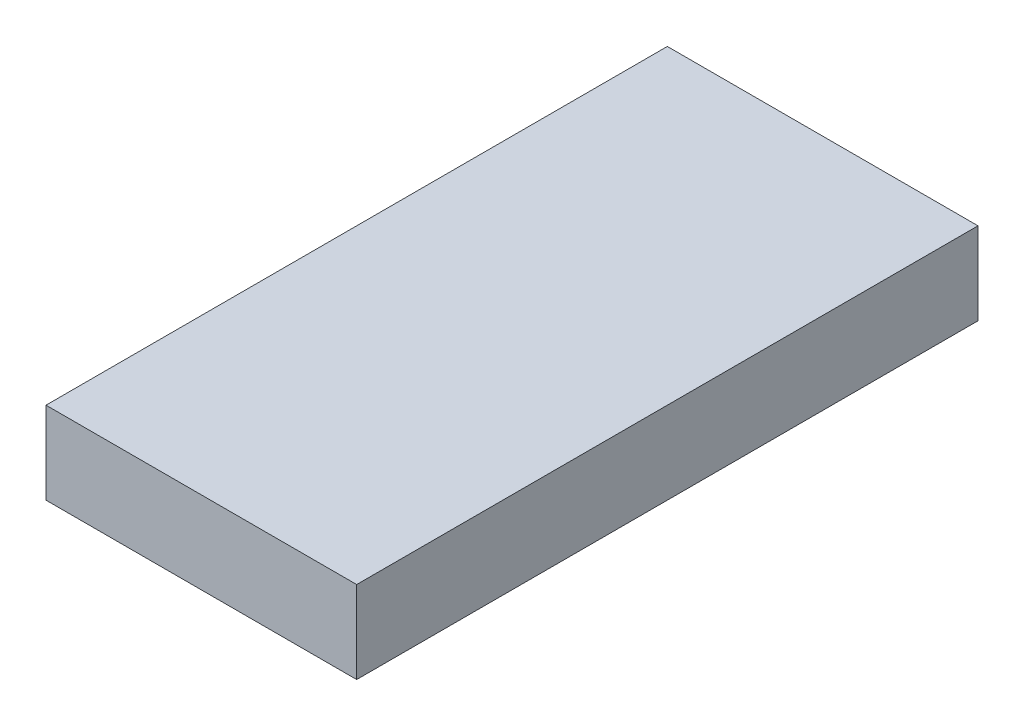
SolidWorks part; units mm, degrees
ref_plane "Front Plane" through (0, 0, 0) normal (0, 0, 1) x (1, 0, 0)
ref_plane "Top Plane" through (0, 0, 0) normal (0, 1, 0) x (1, 0, 0)
ref_plane "Right Plane" through (0, 0, 0) normal (1, 0, 0) x (0, 0, -1)
sketch "Sketch1" plane through (0, 0, 0) normal (0, 1, 0) x (1, 0, 0)
  line L1 (-377.5, -377.5) -> (377.5, -377.5)
  line L2 (-377.5, -377.5) -> (-377.5, 377.5)
  line L3 (-377.5, 377.5) -> (377.5, 377.5)
  line L4 (377.5, -377.5) -> (377.5, 377.5)
  line L5 (-377.5, -377.5) -> (377.5, 377.5) construction
  line L6 (-377.5, 377.5) -> (377.5, -377.5) construction
  point P0 (0, 0)
  dimension "D1" = 755
  dimension "D2" = 755
extrude "Extrude1" add sketch "Sketch1" along normal blind 100
sketch "Sketch2" plane through (0, 100, 0) normal (0, 1, 0) x (1, 0, 0)
  line L0 (0, -423.8245) -> (0, 396.0595)
  line L1 (0, -423.8245) -> (-453.2227, -423.8245)
  line L2 (0, 396.0595) -> (-453.2227, 396.0595)
  line L3 (-453.2227, -423.8245) -> (-453.2227, 396.0595)
extrude "Extrude2" cut sketch "Sketch2" against normal through all
